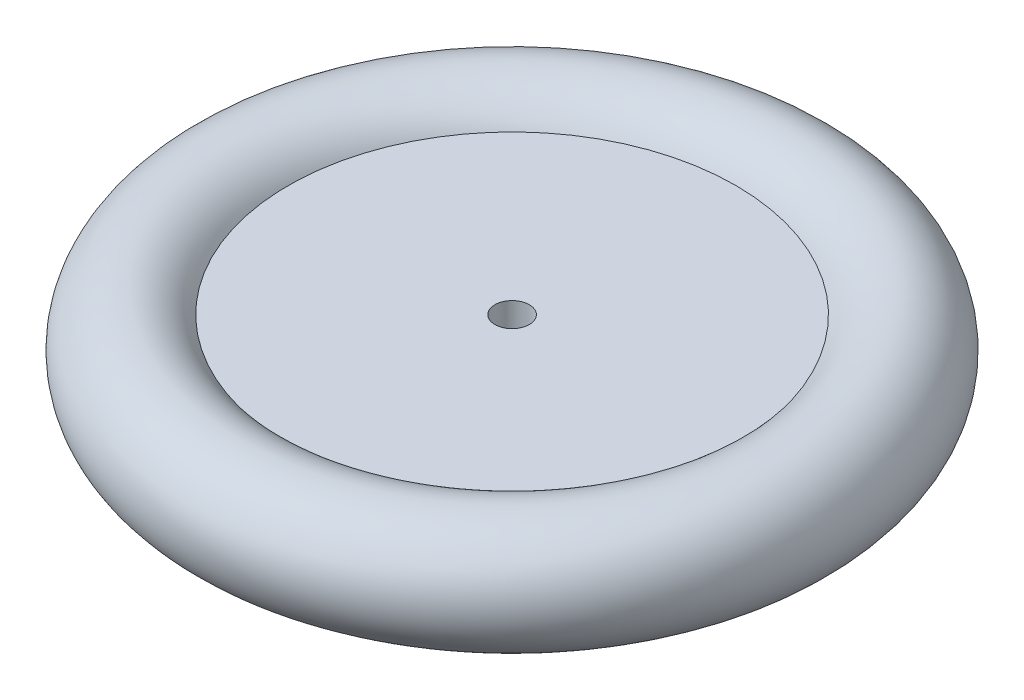
SolidWorks part; units mm, degrees
ref_plane "前视基准面" through (0, 0, 0) normal (0, 0, 1) x (1, 0, 0)
ref_plane "上视基准面" through (0, 0, 0) normal (0, 1, 0) x (1, 0, 0)
ref_plane "右视基准面" through (0, 0, 0) normal (1, 0, 0) x (0, 0, -1)
sketch "草图1" plane through (0, 0, 0) normal (0, 0, 1) x (1, 0, 0)
  line L0 (0, 0) -> (0, 9.5106) construction
  line L1 (1.5, -3) -> (20, -3)
  line L2 (1.5, 3) -> (19.5, 3)
  line L3 (1.5, 3) -> (1.5, -3)
  arc A0 (20, -3) -> (19.5, 3) centre (23.7284, 0.3315) ccw
  dimension "D1" = 6
  dimension "D5" = 5
  dimension "D2" = 3
  dimension "D3" = 1.5
  dimension "D4" = 18
revolve "旋转1" add sketch "草图1" angle 360 about L0
